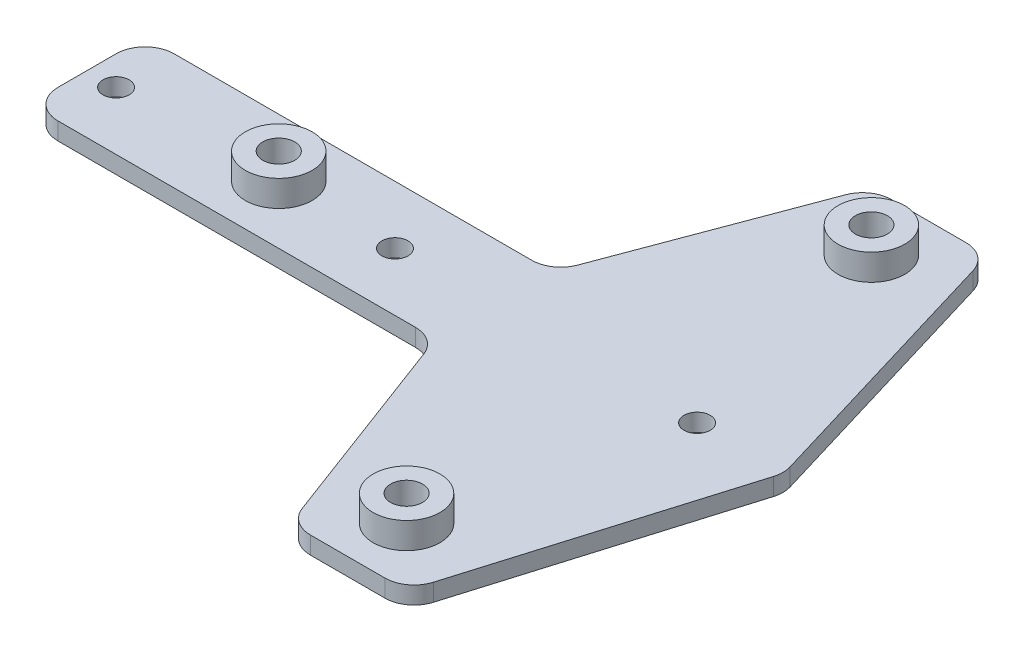
SolidWorks part; units mm, degrees
ref_plane "Front Plane" through (0, 0, 0) normal (0, 0, 1) x (1, 0, 0)
ref_plane "Top Plane" through (0, 0, 0) normal (0, 1, 0) x (1, 0, 0)
ref_plane "Right Plane" through (0, 0, 0) normal (1, 0, 0) x (0, 0, -1)
sketch "Sketch1" plane through (0, 0, 0) normal (0, 1, 0) x (1, 0, 0)
  line L0 (-55, 10) -> (6.535, 10)
  line L1 (11.2166, 13.2444) -> (23.7834, 46.7556)
  line L2 (28.465, 50) -> (41.2798, 50)
  line L3 (46.069, 46.4367) -> (59.569, 1.4367)
  line L4 (59.569, -1.4367) -> (46.069, -46.4367)
  line L5 (41.2798, -50) -> (28.465, -50)
  line L6 (23.7834, -46.7556) -> (11.2166, -13.2444)
  line L7 (6.535, -10) -> (-55, -10)
  line L8 (-60, -5) -> (-60, 5)
  line L9 (-60, 0) -> (60, 0) construction
  line L10 (10, -10) -> (10, 10) construction
  line L11 (25, 50) -> (25, -50) construction
  line L12 (45, -50) -> (45, 50) construction
  arc A0 (6.535, 10) -> (11.2166, 13.2444) centre (6.535, 15) ccw
  arc A1 (23.7834, 46.7556) -> (28.465, 50) centre (28.465, 45) cw
  arc A2 (41.2798, 50) -> (46.069, 46.4367) centre (41.2798, 45) cw
  arc A3 (59.569, 1.4367) -> (59.569, -1.4367) centre (54.7798, 0) cw
  arc A4 (46.069, -46.4367) -> (41.2798, -50) centre (41.2798, -45) cw
  arc A5 (28.465, -50) -> (23.7834, -46.7556) centre (28.465, -45) cw
  arc A6 (11.2166, -13.2444) -> (6.535, -10) centre (6.535, -15) ccw
  arc A7 (-55, -10) -> (-60, -5) centre (-55, -5) cw
  arc A8 (-55, 10) -> (-60, 5) centre (-55, 5) ccw
  point P10 (25, 0)
  point P36 (-60, -10)
  point P39 (-60, 10)
  dimension "D7" = 5
  dimension "D1" = 20
  dimension "D2" = 70
  dimension "D3" = 15
  dimension "D4" = 20
  dimension "D5" = 15
  dimension "D6" = 100
extrude "Boss-Extrude1" add sketch "Sketch1" along normal blind 3
sketch "Sketch2" plane through (0, 3, 0) normal (0, 1, 0) x (1, 0, 0)
  line L0 (-27, 0) -> (0, 0) construction
  line L1 (0, 0) -> (35, 0) construction
  line L2 (35, 40) -> (35, -40) construction
  circle A0 centre (-27, 0) radius 2.75
  circle A1 centre (35, 40) radius 2.75
  circle A2 centre (35, -40) radius 2.75
  dimension "D4" = 5.5
  dimension "D1" = 27
  dimension "D2" = 35
  dimension "D3" = 80
extrude "Cut-Extrude1" cut sketch "Sketch2" against normal through all
sketch "Sketch3" plane through (0, 3, 0) normal (0, 1, 0) x (1, 0, 0)
  circle A0 centre (35, -40) radius 2.75 construction
  circle A1 centre (-27, 0) radius 2.75 construction
  circle A2 centre (35, 40) radius 2.75 construction
  circle A3 centre (35, -40) radius 2.75
  circle A4 centre (-27, 0) radius 2.75
  circle A5 centre (35, 40) radius 2.75
  circle A6 centre (-27, 0) radius 5.75
  circle A7 centre (35, 40) radius 5.75
  circle A8 centre (35, -40) radius 5.75
  dimension "D1" = 3
extrude "Boss-Extrude2" add sketch "Sketch3" along normal blind 4.5
sketch "Sketch4" plane through (0, 3, 0) normal (0, 1, 0) x (1, 0, 0)
  line L0 (-55, 0) -> (0, 0) construction
  line L1 (0, 0) -> (45, 0) construction
  circle A0 centre (-55, 0) radius 2.25
  circle A1 centre (45, 0) radius 2.25
  circle A3 centre (-7, 0) radius 2.25
  dimension "D2" = 4.5
  dimension "D1" = 55
  dimension "D3" = 45
  dimension "D4" = 7
extrude "Cut-Extrude2" cut sketch "Sketch4" against normal through all
